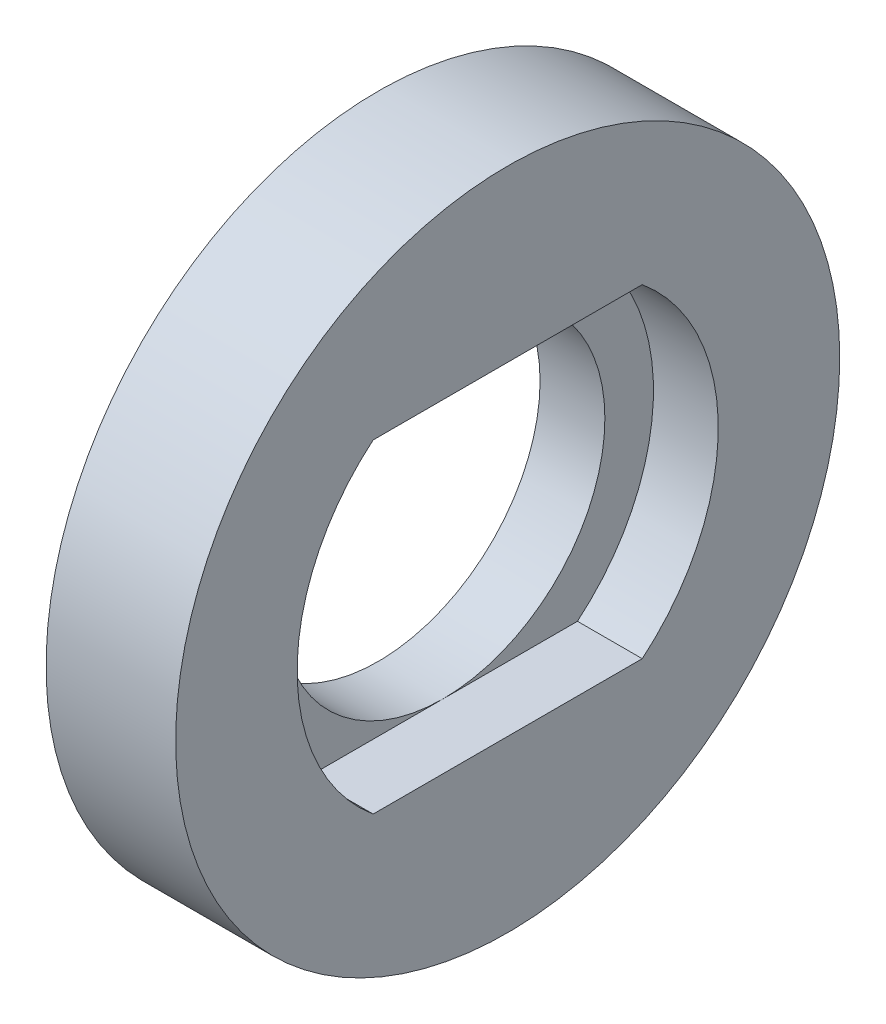
SolidWorks part; units mm, degrees
material "Delrin 2700 NC010, Low Viscosity Acetal Copolymer (SS)"
ref_plane "Front Plane" through (0, 0, 0) normal (0, 0, 1) x (1, 0, 0)
ref_plane "Top Plane" through (0, 0, 0) normal (0, 1, 0) x (1, 0, 0)
ref_plane "Right Plane" through (0, 0, 0) normal (1, 0, 0) x (0, 0, -1)
sketch "Sketch1" plane through (0, 0, 0) normal (1, 0, 0) x (0, 0, -1)
  circle A0 centre (0, 0) radius 10.25
  dimension "D1" = 20.5
extrude "Boss-Extrude1" add sketch "Sketch1" along normal blind 4
sketch "Sketch2" plane through (4, 0, 0) normal (1, 0, 0) x (0, 0, -1)
  line L1 (-4.1533, -5) -> (4.1533, -5)
  line L2 (-4.1533, -5) -> (-4.1533, 5)
  line L3 (-4.1533, 5) -> (4.1533, 5)
  line L4 (4.1533, -5) -> (4.1533, 5)
  line L5 (-4.1533, -5) -> (4.1533, 5) construction
  line L6 (-4.1533, 5) -> (4.1533, -5) construction
  circle A0 centre (0, 0) radius 6.5
  dimension "D1" = 13
  dimension "D2" = 10
extrude "Cut-Extrude1" cut sketch "Sketch2" against normal blind 2 contours L2 A0 | L1 L4 L3 L2 | L4 A0
sketch "Sketch3" plane through (2, 0, 0) normal (1, 0, 0) x (0, 0, -1)
  circle A0 centre (0, 0) radius 5
  dimension "D1" = 10
extrude "Cut-Extrude2" cut sketch "Sketch3" against normal through all
